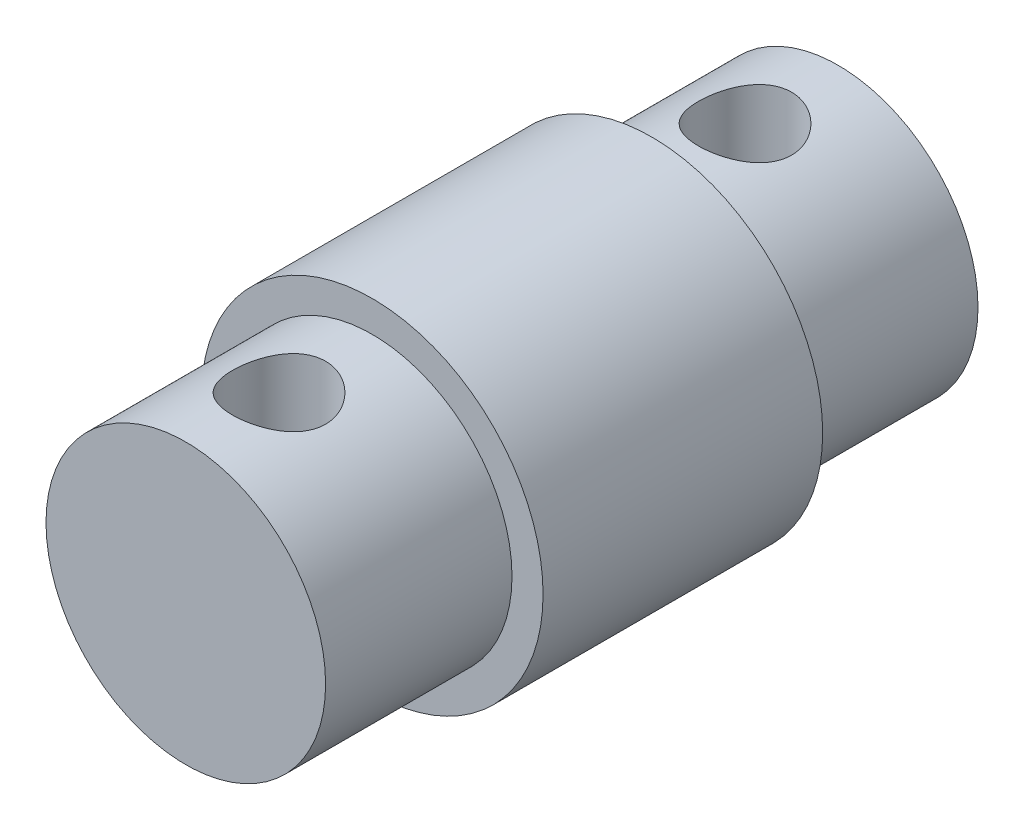
SolidWorks part; units mm, degrees
material "AISI 304"
ref_plane "Front Plane" through (0, 0, 0) normal (0, 0, 1) x (1, 0, 0)
ref_plane "Top Plane" through (0, 0, 0) normal (0, 1, 0) x (1, 0, 0)
ref_plane "Right Plane" through (0, 0, 0) normal (1, 0, 0) x (0, 0, -1)
sketch "Sketch1" plane through (0, 0, 0) normal (0, 0, 1) x (1, 0, 0)
  circle A0 centre (0, 0) radius 5.5
extrude "Boss-Extrude1" add sketch "Sketch1" along normal blind 9
sketch "Sketch2" plane through (0, 0, 9) normal (0, 0, 1) x (1, 0, 0)
  circle A0 centre (0, 0) radius 4.5
  dimension "D1" = 9
extrude "Boss-Extrude2" add sketch "Sketch2" along normal blind 6
sketch "Sketch3" plane through (0, 0, 0) normal (0, 0, -1) x (-1, 0, 0)
  circle A0 centre (0, 0) radius 4.5
extrude "Boss-Extrude3" add sketch "Sketch3" along normal blind 6
sketch "Sketch4" plane through (0, 0, 0) normal (0, 1, 0) x (1, 0, 0)
  line L0 (-4.5, -15) -> (4.5, -15) construction
  line L1 (4.5, 6) -> (-4.5, 6) construction
  circle A0 centre (0, 3) radius 1.5
  circle A1 centre (0, -12) radius 1.5
  dimension "D1" = 3
  dimension "D2" = 3
extrude "Cut-Extrude1" cut sketch "Sketch4" against normal through all both and the other way through all
